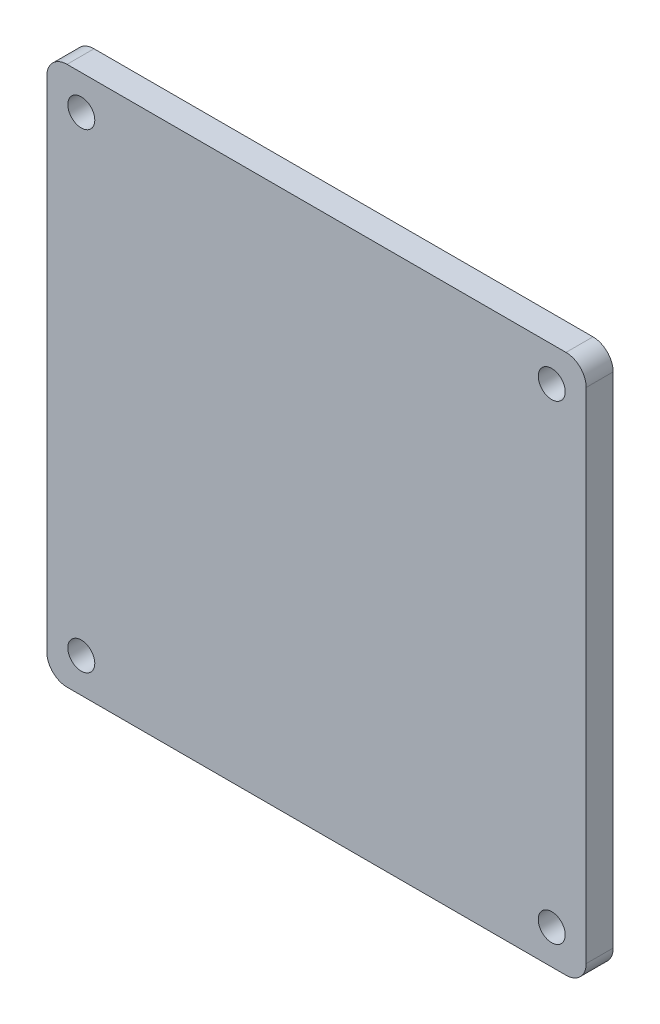
SolidWorks part; units mm, degrees
ref_plane "前视基准面" through (0, 0, 0) normal (0, 0, 1) x (1, 0, 0)
ref_plane "上视基准面" through (0, 0, 0) normal (0, 1, 0) x (1, 0, 0)
ref_plane "右视基准面" through (0, 0, 0) normal (1, 0, 0) x (0, 0, -1)
sketch "草图1" plane through (0, 0, 0) normal (0, 0, 1) x (1, 0, 0)
  line L1 (-18.5, -20) -> (18.5, -20)
  line L2 (-20, -18.5) -> (-20, 18.5)
  line L3 (-18.5, 20) -> (18.5, 20)
  line L4 (20, -18.5) -> (20, 18.5)
  circle A2 centre (-17.4424, 17.4424) radius 1
  circle A3 centre (17.4424, 17.4424) radius 1
  circle A4 centre (17.4424, -17.4424) radius 1
  circle A5 centre (-17.4424, -17.4424) radius 1
  arc A6 (-18.5, -20) -> (-20, -18.5) centre (-18.5, -18.5) cw
  arc A7 (18.5, -20) -> (20, -18.5) centre (18.5, -18.5) ccw
  arc A8 (20, 18.5) -> (18.5, 20) centre (18.5, 18.5) ccw
  arc A9 (-20, 18.5) -> (-18.5, 20) centre (-18.5, 18.5) cw
  point P0 (0, 0)
  point P6 (0, 0)
  dimension "D7" = 2
  dimension "D9" = 1.5
  dimension "D8" = 4
extrude "凸台-拉伸1" add sketch "草图1" along normal blind 2
